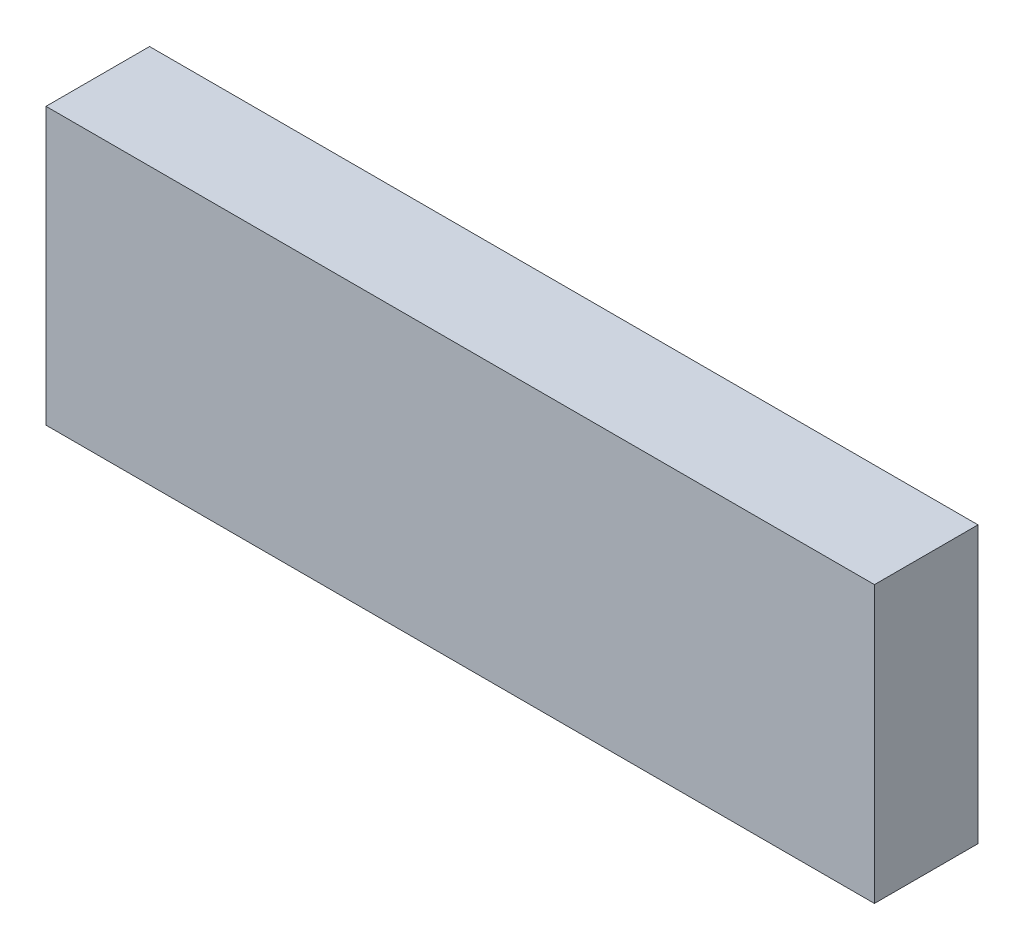
SolidWorks part; units mm, degrees
material "Стекло"
ref_plane "Спереди" through (0, 0, 0) normal (0, 0, 1) x (1, 0, 0)
ref_plane "Сверху" through (0, 0, 0) normal (0, 1, 0) x (1, 0, 0)
ref_plane "Справа" through (0, 0, 0) normal (1, 0, 0) x (0, 0, -1)
sketch "Эскиз1" plane through (0, 0, 0) normal (0, 0, 1) x (1, 0, 0)
  line L1 (7.8479, -18.5) -> (-16.1521, -18.5)
  line L2 (7.8479, -18.5) -> (7.8479, -10.5)
  line L3 (7.8479, -10.5) -> (-16.1521, -10.5)
  line L4 (-16.1521, -18.5) -> (-16.1521, -10.5)
  dimension "D1" = 8
  dimension "D2" = 24
extrude "Вытянуть1" add sketch "Эскиз1" along normal blind 3
chamfer "Фаска1" [suppressed] distance 0.3 angle 45
ref_point "Точка1"
